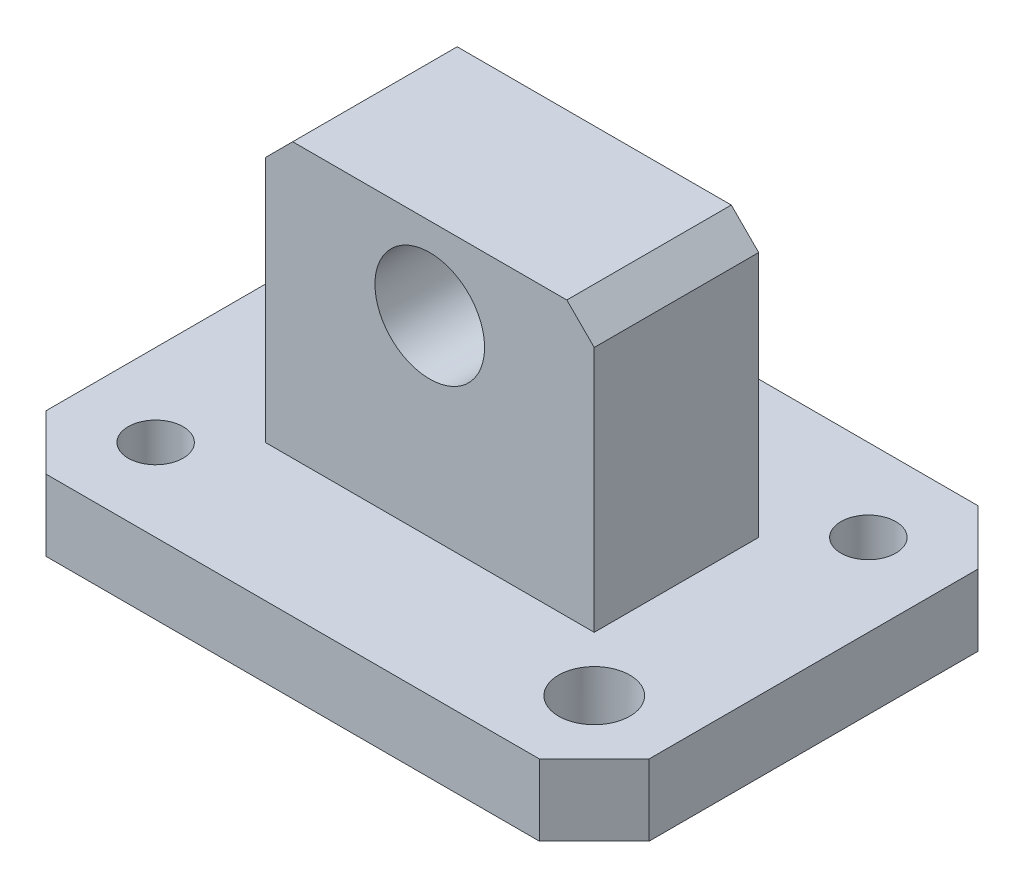
SolidWorks part; units mm, degrees
ref_plane "Спереди" through (0, 0, 0) normal (0, 0, 1) x (1, 0, 0)
ref_plane "Сверху" through (0, 0, 0) normal (0, 1, 0) x (1, 0, 0)
ref_plane "Справа" through (0, 0, 0) normal (1, 0, 0) x (0, 0, -1)
sketch "Эскиз1" plane through (0, 0, 0) normal (0, 1, 0) x (1, 0, 0)
  line L0 (0, 70) -> (10, 80)
  line L1 (10, 0) -> (100, 0)
  line L2 (0, 10) -> (0, 70)
  line L3 (10, 80) -> (100, 80)
  line L4 (110, 10) -> (110, 70)
  line L5 (110, 70) -> (100, 80)
  line L6 (100, 0) -> (110, 10)
  line L7 (10, 0) -> (0, 10)
  point P0 (0, 0)
  point P1 (110, 80)
  point P2 (0, 80)
  point P3 (110, 0)
  dimension "D1" = 80
  dimension "D2" = 110
extrude "Бобышка-Вытянуть1" add sketch "Эскиз1" along normal blind 13
sketch "Эскиз3" plane through (0, 13, 0) normal (0, 1, 0) x (1, 0, 0)
  line L0 (55, 83.6901) -> (55, -3.5709) construction
  line L1 (-3.174, 40) -> (113.0548, 40) construction
  line L2 (100, 80) -> (10, 80) construction
  line L3 (25, 55) -> (85, 55)
  line L4 (25, 55) -> (25, 25)
  line L5 (25, 25) -> (85, 25)
  line L6 (85, 55) -> (85, 25)
  line L7 (0, 70) -> (0, 10) construction
  dimension "D1" = 15
  dimension "D2" = 40
  dimension "D3" = 55
  dimension "D4" = 15
  dimension "D5" = 30
  dimension "D6" = 30
extrude "Бобышка-Вытянуть2" add sketch "Эскиз3" along normal blind 50
chamfer "Фаска1" distance 5 angle 45 2 edges at (25, 63, -40) (85, 63, -40)
sketch "Эскиз4" plane through (0, 13, 0) normal (0, 1, 0) x (1, 0, 0)
  line L0 (17.6875, 40) -> (90.5243, 40) construction
  line L1 (55, 58.0602) -> (55, 20.1517) construction
  line L2 (0, 70) -> (0, 10) construction
  line L3 (100, 80) -> (10, 80) construction
  circle A0 centre (15, 65) radius 6.5
  circle A1 centre (95, 15) radius 6.5
  circle A2 centre (95, 65) radius 5
  circle A3 centre (15, 15) radius 5
  dimension "D7" = 13
  dimension "D8" = 13
  dimension "D9" = 10
  dimension "D10" = 10
  dimension "D1" = 55
  dimension "D2" = 40
  dimension "D3" = 25
  dimension "D4" = 40
  dimension "D5" = 25
  dimension "D6" = 40
extrude "Вырез-Вытянуть1" cut sketch "Эскиз4" against normal blind 50
sketch "Эскиз5" plane through (0, 0, -25) normal (0, 0, 1) x (1, 0, 0)
  line L0 (10, 0) -> (100, 0) construction
  circle A0 centre (55, 48) radius 10
  dimension "D2" = 20
  dimension "D1" = 48
extrude "Вырез-Вытянуть2" cut sketch "Эскиз5" against normal blind 50
